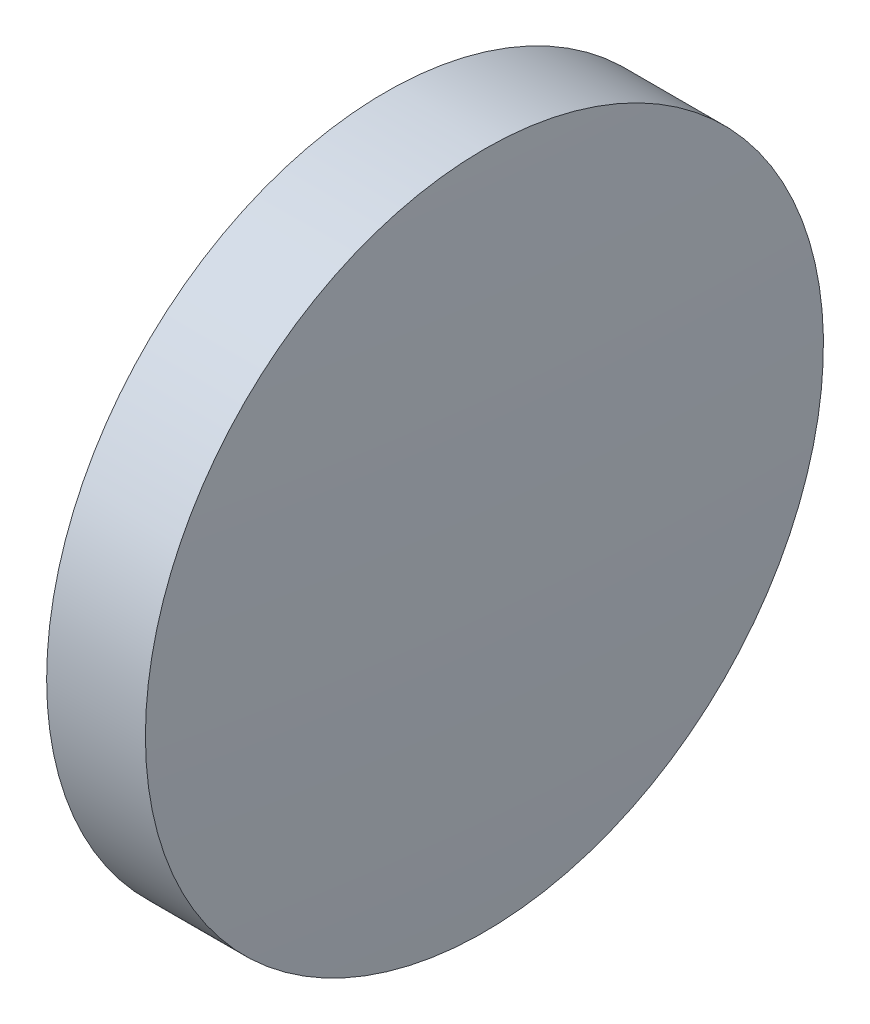
SolidWorks part; units mm, degrees
ref_plane "前视基准面" through (0, 0, 0) normal (0, 0, 1) x (1, 0, 0)
ref_plane "上视基准面" through (0, 0, 0) normal (0, 1, 0) x (1, 0, 0)
ref_plane "右视基准面" through (0, 0, 0) normal (1, 0, 0) x (0, 0, -1)
sketch "草图1" plane through (0, 0, 0) normal (0, 0, 1) x (1, 0, 0)
  line L0 (538.7658, 475.3742) -> (557.5617, 475.3742) construction
  line L1 (544.3957, 475.3742) -> (544.3957, 488.0742)
  line L2 (548.3957, 475.3742) -> (544.3957, 475.3742)
  line L5 (544.3957, 488.0742) -> (548.0957, 488.0742)
  arc A0 (548.3957, 475.3742) -> (548.0957, 488.0742) centre (279.429, 475.3742) ccw
revolve "旋转1" add sketch "草图1" angle 360 about L0
